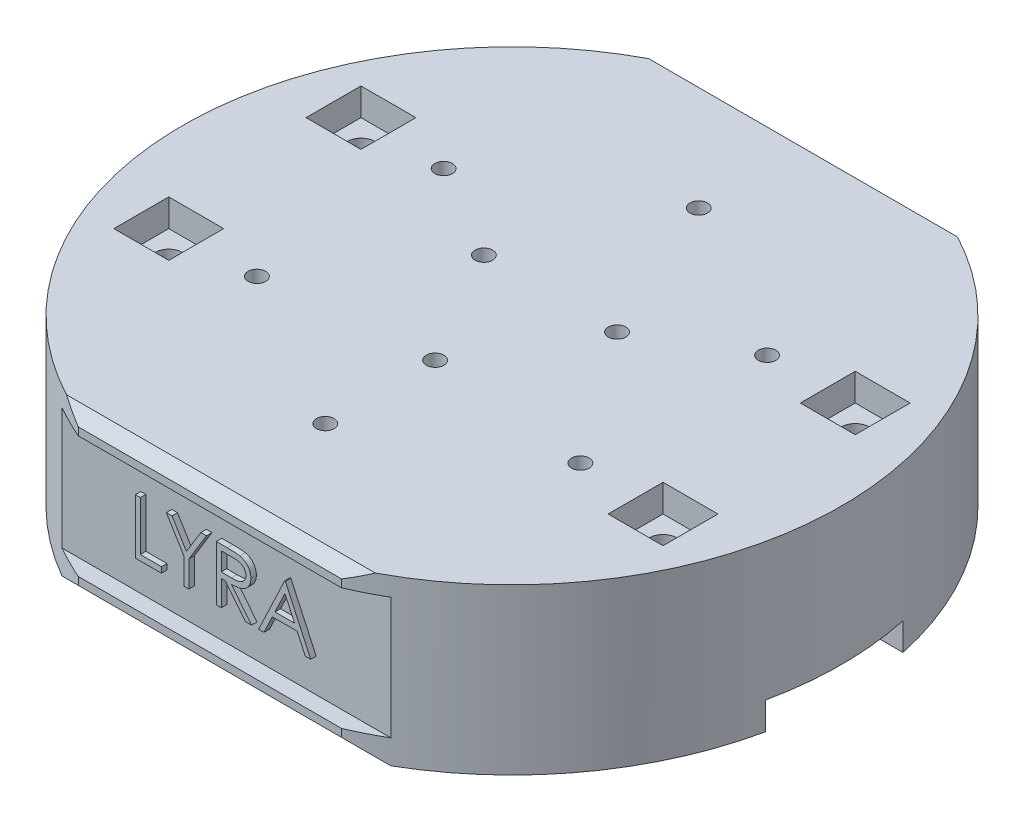
SolidWorks part; units mm, degrees
ref_plane "Front Plane" through (0, 0, 0) normal (0, 0, 1) x (1, 0, 0)
ref_plane "Top Plane" through (0, 0, 0) normal (0, 1, 0) x (1, 0, 0)
ref_plane "Right Plane" through (0, 0, 0) normal (1, 0, 0) x (0, 0, -1)
sketch "Sketch2" plane through (0, 0, 0) normal (0, 1, 0) x (1, 0, 0)
  line L0 (52.3244, 55) -> (70, 40.2836)
  line L5 (52.3244, 55) -> (-52.3244, 55)
  line L6 (0, 0) -> (0, 93.3985) construction
  line L7 (-52.3244, 55) -> (-70, 40.2836)
  line L8 (-70, -40.2836) -> (-52.3244, -55)
  line L9 (70, -40.2836) -> (52.3244, -55)
  line L10 (70, 40.2836) -> (70, -40.2836)
  line L11 (-70, 40.2836) -> (-70, -40.2836)
  line L12 (-52.3244, -55) -> (52.3244, -55)
  dimension "D2" = 23
  dimension "D3" = 140
  dimension "D6" = 23
  dimension "D7" = 23
  dimension "D8" = 23
extrude "Boss-Extrude3" add sketch "Sketch2" along normal blind 30
chamfer "Chamfer3" distance 2 angle 45 8 edges at (-61.1622, 30, -47.6418) (0, 30, -55) (61.1622, 30, -47.6418) (70, 30, 0) (61.1622, 30, 47.6418) (0, 30, 55) (-61.1622, 30, 47.6418) (-70, 30, 0)
chamfer "Chamfer4" distance 3 angle 45 8 edges at (-61.1622, 0, 47.6418) (0, 0, 55) (61.1622, 0, 47.6418) (70, 0, 0) (61.1622, 0, -47.6418) (0, 0, -55) (-61.1622, 0, -47.6418) (-70, 0, 0)
sketch "Sketch5" plane through (0, 0, 0) normal (0, -1, 0) x (1, 0, 0)
  circle A0 centre (0, 0) radius 40
  dimension "D1" = 80
extrude "Cut-Extrude1" cut sketch "Sketch5" against normal blind 10
chamfer "Chamfer5" distance 1 angle 45 1 edges at (0, 0, -40)
sketch "Sketch8" plane through (0, 0, 55) normal (0, 0, 1) x (1, 0, 0)
  line L0 (-52.3244, 28) -> (-50.9102, 26.5858)
  line L1 (-52.3244, 28) -> (-52.3244, 3) construction
  line L2 (-50.9102, 26.5858) -> (-50.9102, 4.4142)
  line L3 (-50.9102, 4.4142) -> (-52.3244, 3)
  line L4 (-50.9102, 4.4142) -> (50.9102, 4.4142)
  line L5 (50.9102, 4.4142) -> (52.3244, 3)
  line L6 (50.9102, 4.4142) -> (50.9102, 26.5858)
  line L7 (50.9102, 26.5858) -> (52.3244, 28)
  line L8 (50.9102, 26.5858) -> (-50.9102, 26.5858)
  dimension "D1" = 45
  dimension "D2" = 2
  dimension "D3" = 2
  dimension "D4" = 2
  dimension "D5" = 2
extrude "Cut-Extrude5" cut sketch "Sketch8" against normal blind 3 contours L6 L8 L2 L4
sketch "Sketch9" plane through (0, 0, 0) normal (0, -1, 0) x (1, 0, 0)
  line L0 (37.9967, 12.5) -> (70, 12.5)
  line L1 (70, 40.2836) -> (70, -40.2836) construction
  line L2 (37.9967, -12.5) -> (70, -12.5)
  line L3 (70, 12.5) -> (70, -12.5)
  line L4 (0, 0) -> (0, 13.817) construction
  line L5 (-37.9967, 12.5) -> (-70, 12.5)
  line L6 (-70, 12.5) -> (-70, -12.5)
  line L7 (-37.9967, -12.5) -> (-70, -12.5)
  line L8 (51.239, 52) -> (-51.239, 52)
  line L9 (-51.239, 52) -> (-67, 38.8776)
  line L10 (-67, 38.8776) -> (-67, -38.8776)
  line L11 (-67, -38.8776) -> (-51.239, -52)
  line L12 (-51.239, -52) -> (51.239, -52)
  line L13 (51.239, -52) -> (67, -38.8776)
  line L14 (67, -38.8776) -> (67, 38.8776)
  line L15 (67, 38.8776) -> (51.239, 52)
  line L16 (51.239, 52) -> (-51.239, 52)
  line L17 (-51.239, 52) -> (-67, 38.8776)
  line L18 (-67, 38.8776) -> (-67, -38.8776)
  line L19 (-67, -38.8776) -> (-51.239, -52)
  line L20 (-51.239, -52) -> (51.239, -52)
  line L21 (51.239, -52) -> (67, -38.8776)
  line L22 (67, -38.8776) -> (67, 38.8776)
  line L23 (67, 38.8776) -> (51.239, 52)
  arc A2 (37.9967, 12.5) -> (37.9967, -12.5) centre (0, 0) cw
  arc A3 (-37.9967, 12.5) -> (-37.9967, -12.5) centre (0, 0) ccw
  circle M9 centre (0, 0) radius 41
  line M16 (67, -38.8776) -> (67, 38.8776)
  dimension "D2" = 25
  dimension "D1" = 0
extrude "Cut-Extrude7" cut sketch "Sketch9" against normal blind 5 contours L2 L0 M9 M16 | L3 L0 L2 M16 | L0 A2 L2 M9 | L5 L6 L7 A3
sketch "Sketch11" plane through (0, 0, -55) normal (0, 0, -1) x (-1, 0, 0)
  line L0 (-52.3244, 28) -> (-50.9102, 26.5858)
  line L1 (-50.9102, 26.5858) -> (-50.9102, 4.4142)
  line L2 (-50.9102, 4.4142) -> (-52.3244, 3)
  line L3 (-52.3244, 3) -> (52.3244, 3) construction
  line L4 (-52.3244, 28) -> (-52.3244, 3) construction
  line L5 (-50.9102, 26.5858) -> (50.9102, 26.5858)
  line L6 (50.9102, 26.5858) -> (52.3244, 28)
  line L7 (52.3244, 28) -> (-52.3244, 28) construction
  line L8 (50.9102, 26.5858) -> (50.9102, 4.4142)
  line L9 (50.9102, 4.4142) -> (-50.9102, 4.4142)
  line L10 (50.9102, 4.4142) -> (52.3244, 3)
  dimension "D1" = 2
  dimension "D2" = 2
  dimension "D3" = 2
  dimension "D4" = 2
extrude "Cut-Extrude9" cut sketch "Sketch11" against normal blind 3 contours L9 L8 L5 L1
sketch "Sketch12" plane through (0, 10, 0) normal (0, -1, 0) x (1, 0, 0)
  circle A0 centre (0, 0) radius 41
  dimension "D1" = 82
extrude "Cut-Extrude13" cut sketch "Sketch12" against normal blind 10 and the other way blind 10
chamfer "Chamfer7" distance 1 angle 45 1 edges at (0, 0, -41)
sketch "Sketch13" plane through (0, 20, 0) normal (0, -1, 0) x (1, 0, 0)
  circle A1 centre (0, 14) radius 1.6
  circle A2 centre (12.1244, -7) radius 1.6
  circle A3 centre (-12.1244, -7) radius 1.6
  point P13 (0, 0)
  dimension "D2" = 3.2
  dimension "D3" = 3
extrude "Cut-Extrude14" cut sketch "Sketch13" against normal blind 20
sketch "Sketch14" plane through (0, 20, 0) normal (0, -1, 0) x (1, 0, 0)
  circle A1 centre (0, 34) radius 1.6
  circle A2 centre (29.4449, 17) radius 1.6
  circle A3 centre (29.4449, -17) radius 1.6
  circle A4 centre (0, -34) radius 1.6
  circle A5 centre (-29.4449, -17) radius 1.6
  circle A6 centre (-29.4449, 17) radius 1.6
  point P20 (0, 0)
  dimension "D2" = 3.2
  dimension "D3" = 6
extrude "Cut-Extrude15" cut sketch "Sketch14" against normal blind 20
sketch "Sketch18" plane through (0, 30, 0) normal (0, 1, 0) x (1, 0, 0)
  circle A0 centre (0, 0) radius 60
  dimension "D1" = 120
extrude "Cut-Extrude16" cut sketch "Sketch18" against normal blind 60 flip side to cut
sketch "Sketch19" plane through (0, 0, 52) normal (0, 0, 1) x (1, 0, 0)
  line L0 (-29.9333, 10.5) -> (29.9333, 10.5) construction
  line L1 (29.9333, 4.4142) -> (29.9333, 26.5858) construction
  line L2 (-29.9333, 26.5858) -> (-29.9333, 4.4142) construction
  text T0 "LYRA" font "Century Gothic" height 10
  point P5 (-29.9333, 15.5)
  dimension "D1" = 5
extrude "Boss-Extrude6" add sketch "Sketch19" along normal blind 1
sketch "Sketch21" plane through (0, 30, 0) normal (0, 1, 0) x (1, 0, 0)
  line L0 (0, 0) -> (7.3623, 0) construction
  line L1 (40, 12.5) -> (50, 12.5)
  line L8 (0, 0) -> (0, 12.5599) construction
  line L23 (-50, -12.5) -> (-40, -12.5)
  line L24 (-50, 12.5) -> (-40, 12.5)
  line L25 (40, -12.5) -> (50, -12.5)
  line L31 (40, 12.5) -> (40, 22.5)
  line L32 (40, 22.5) -> (50, 22.5)
  line L33 (50, 22.5) -> (50, 12.5)
  line L36 (40, -12.5) -> (40, -22.5)
  line L37 (40, -22.5) -> (50, -22.5)
  line L38 (50, -22.5) -> (50, -12.5)
  line L41 (-50, -22.5) -> (-50, -12.5)
  line L46 (-50, 22.5) -> (-50, 12.5)
  line L47 (-40, 22.5) -> (-50, 22.5)
  line L48 (-40, 12.5) -> (-40, 22.5)
  line L50 (-50, -22.5) -> (-40, -22.5)
  line L51 (-40, -22.5) -> (-40, -12.5)
  dimension "D4" = 10
  dimension "D6" = 10
  dimension "D8" = 10
  dimension "D9" = 10
extrude "Cut-Extrude20" cut sketch "Sketch21" against normal blind 5
sketch "Sketch24" plane through (0, 30, 0) normal (0, 1, 0) x (1, 0, 0)
  line L0 (0, 0) -> (-45, 0)
  line L1 (-45, 0) -> (-45, 17.5)
  line L2 (0, 0) -> (4.7161, 0) construction
  line L3 (0, 0) -> (0, 7.489) construction
  circle A0 centre (-45, 17.5) radius 2.5
  circle A1 centre (45, 17.5) radius 2.5
  circle A2 centre (45, -17.5) radius 2.5
  circle A3 centre (-45, -17.5) radius 2.5
  dimension "D3" = 5
  dimension "D1" = 45
  dimension "D2" = 17.5
extrude "Cut-Extrude22" cut sketch "Sketch24" against normal blind 12
sketch "Sketch22" plane through (0, 30, 0) normal (0, 1, 0) x (1, 0, 0)
  line L0 (0, 0) -> (0, 24.3166) construction
  circle A0 centre (-25, 0) radius 2.5
  circle A1 centre (25, 0) radius 2.5
  dimension "D2" = 5
